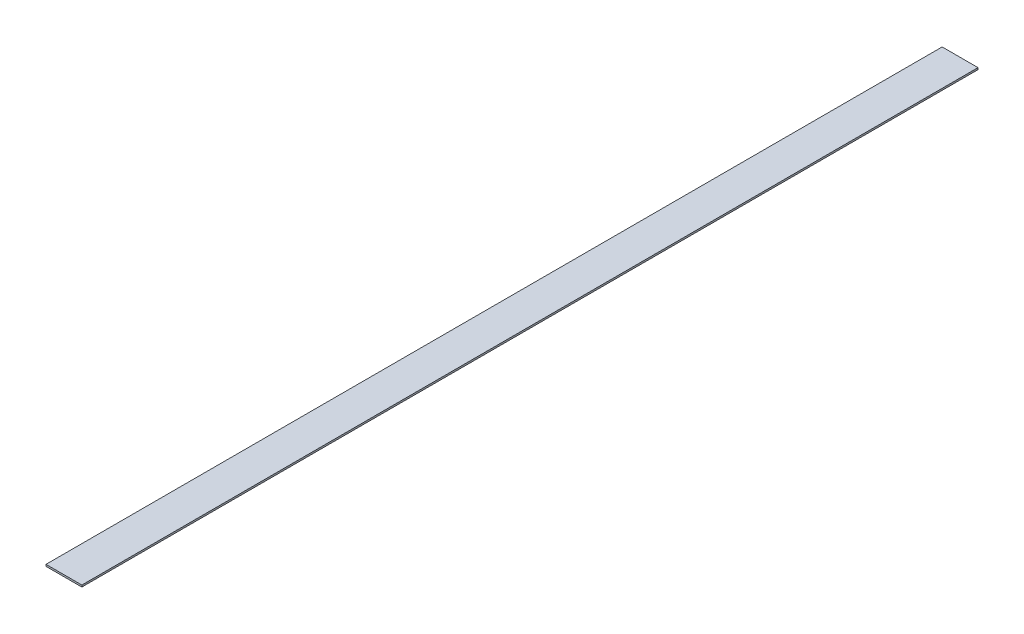
SolidWorks part; units mm, degrees
ref_plane "Plan de face" through (0, 0, 0) normal (0, 0, 1) x (1, 0, 0)
ref_plane "Plan de dessus" through (0, 0, 0) normal (0, 1, 0) x (1, 0, 0)
ref_plane "Plan de droite" through (0, 0, 0) normal (1, 0, 0) x (0, 0, -1)
sketch "Esquisse1" plane through (0, 0, 0) normal (0, 1, 0) x (1, 0, 0)
  line L0 (-10, 0) -> (10, 0) construction
  line L1 (-10, -250) -> (10, -250)
  line L2 (-10, -250) -> (-10, 250)
  line L3 (-10, 250) -> (10, 250)
  line L4 (10, -250) -> (10, 250)
  point P6 (0, 0)
  dimension "D1" = 20
  dimension "D2" = 500
extrude "Boss.-Extru.1" add sketch "Esquisse1" along normal blind 1
fillet "Congé1" [suppressed] radius 5
